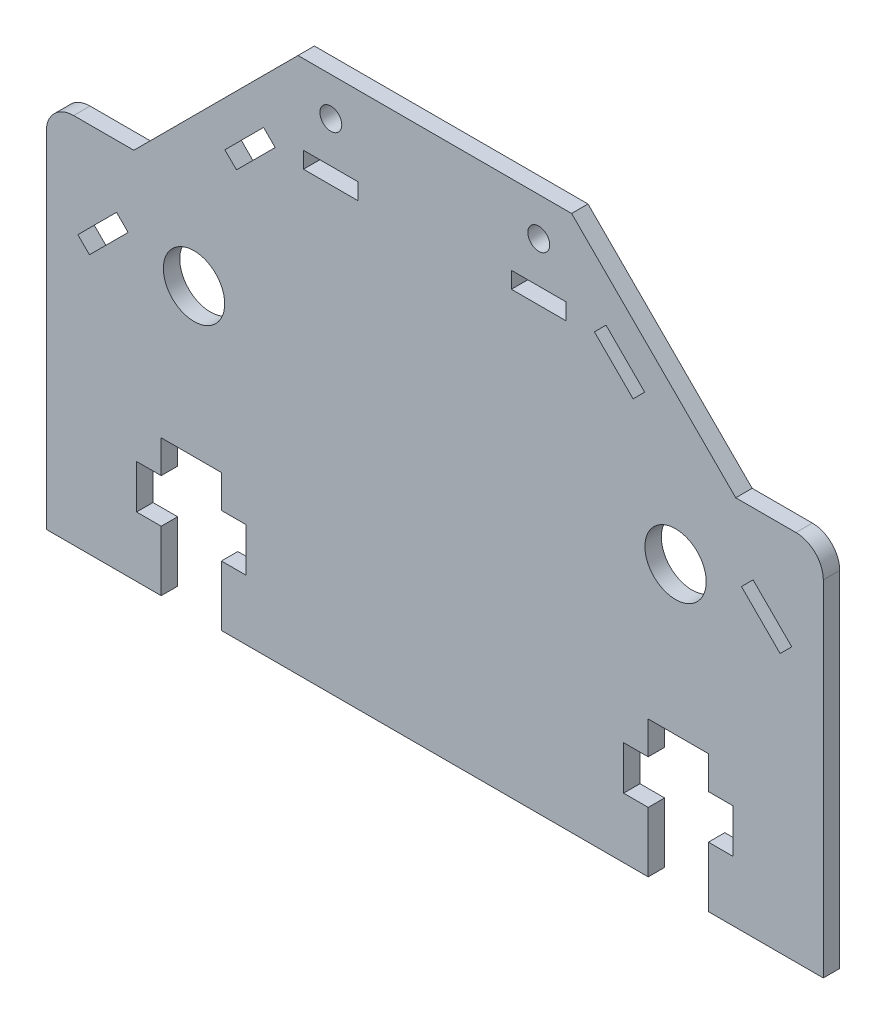
SolidWorks part; units mm, degrees
ref_plane "Alzado" through (0, 0, 0) normal (0, 0, 1) x (1, 0, 0)
ref_plane "Planta" through (0, 0, 0) normal (0, 1, 0) x (1, 0, 0)
ref_plane "Vista lateral" through (0, 0, 0) normal (1, 0, 0) x (0, 0, -1)
sketch "Model" plane through (0, 0, 0) normal (0, 0, 1) x (1, 0, 0)
  line L0 (-237.0746, -49.6716) -> (-258.0746, -49.6716)
  line L1 (-137.0746, -49.6716) -> (-116.0746, -49.6716)
  line L2 (-226.0746, -49.6716) -> (-148.0746, -49.6716)
  line L3 (-258.0746, 13.3284) -> (-258.0746, -49.6716)
  line L4 (-116.0746, 13.3284) -> (-116.0746, -49.6716)
  line L5 (-157.9053, 31.6738) -> (-150.8342, 24.6028)
  line L6 (-250.1851, -2.2673) -> (-243.114, 4.8038)
  line L7 (-211.0746, 30.8284) -> (-201.0746, 30.8284)
  line L8 (-123.9642, -2.2673) -> (-131.0352, 4.8038)
  line L9 (-216.2439, 31.6738) -> (-223.315, 24.6028)
  line L10 (-163.0746, 30.8284) -> (-173.0746, 30.8284)
  line L11 (-243.114, 4.8038) -> (-245.2353, 6.9251)
  line L12 (-131.0352, 4.8038) -> (-128.9139, 6.9251)
  line L13 (-150.8342, 24.6028) -> (-148.7129, 26.7241)
  line L14 (-201.0746, 30.8284) -> (-201.0746, 33.8284)
  line L15 (-223.315, 24.6028) -> (-225.4363, 26.7241)
  line L16 (-173.0746, 30.8284) -> (-173.0746, 33.8284)
  line L17 (-162.0746, 48.3284) -> (-132.0746, 18.3284)
  line L18 (-212.0746, 48.3284) -> (-242.0746, 18.3284)
  line L19 (-128.9139, 6.9251) -> (-121.8428, -0.146)
  line L20 (-225.4363, 26.7241) -> (-218.3653, 33.7951)
  line L21 (-173.0746, 33.8284) -> (-163.0746, 33.8284)
  line L22 (-148.7129, 26.7241) -> (-155.784, 33.7951)
  line L23 (-245.2353, 6.9251) -> (-252.3064, -0.146)
  line L24 (-201.0746, 33.8284) -> (-211.0746, 33.8284)
  line L25 (-121.8428, -0.146) -> (-123.9642, -2.2673)
  line L26 (-252.3064, -0.146) -> (-250.1851, -2.2673)
  line L27 (-218.3653, 33.7951) -> (-216.2439, 31.6738)
  line L28 (-163.0746, 33.8284) -> (-163.0746, 30.8284)
  line L29 (-155.784, 33.7951) -> (-157.9053, 31.6738)
  line L30 (-211.0746, 33.8284) -> (-211.0746, 30.8284)
  line L31 (-132.5746, -38.6716) -> (-137.0746, -38.6716)
  line L32 (-241.5746, -38.6716) -> (-237.0746, -38.6716)
  line L33 (-152.5746, -38.6716) -> (-152.5746, -30.6716)
  line L34 (-221.5746, -38.6716) -> (-221.5746, -30.6716)
  line L35 (-137.0746, -30.6716) -> (-132.5746, -30.6716)
  line L36 (-237.0746, -30.6716) -> (-241.5746, -30.6716)
  line L37 (-132.5746, -30.6716) -> (-132.5746, -38.6716)
  line L38 (-241.5746, -30.6716) -> (-241.5746, -38.6716)
  line L39 (-137.0746, -49.6716) -> (-137.0746, -38.6716)
  line L40 (-137.0746, -30.6716) -> (-137.0746, -24.6716)
  line L41 (-237.0746, -49.6716) -> (-237.0746, -38.6716)
  line L42 (-237.0746, -30.6716) -> (-237.0746, -24.6716)
  line L43 (-148.0746, -49.6716) -> (-148.0746, -38.6716)
  line L44 (-148.0746, -30.6716) -> (-148.0746, -24.6716)
  line L45 (-226.0746, -49.6716) -> (-226.0746, -38.6716)
  line L46 (-226.0746, -30.6716) -> (-226.0746, -24.6716)
  line L47 (-148.0746, -38.6716) -> (-152.5746, -38.6716)
  line L48 (-226.0746, -38.6716) -> (-221.5746, -38.6716)
  line L49 (-132.0746, 18.3284) -> (-121.0746, 18.3284)
  line L50 (-242.0746, 18.3284) -> (-253.0746, 18.3284)
  line L51 (-162.0746, 48.3284) -> (-212.0746, 48.3284)
  line L52 (-137.0746, -24.6716) -> (-148.0746, -24.6716)
  line L53 (-237.0746, -24.6716) -> (-226.0746, -24.6716)
  line L54 (-148.0746, -30.6716) -> (-152.5746, -30.6716)
  line L55 (-226.0746, -30.6716) -> (-221.5746, -30.6716)
  circle A0 centre (-231.0746, 2.3284) radius 5.6027
  circle A1 centre (-143.0746, 2.3284) radius 5.6027
  arc A2 (-116.0746, 13.3284) -> (-121.0746, 18.3284) centre (-121.0746, 13.3284) ccw
  arc A3 (-253.0746, 18.3284) -> (-258.0746, 13.3284) centre (-253.0746, 13.3284) ccw
  circle A4 centre (-168.0746, 41.3284) radius 2
  circle A5 centre (-206.0746, 41.3284) radius 2
extrude "Saliente-Extruir1" add sketch "Model" along normal blind 3
